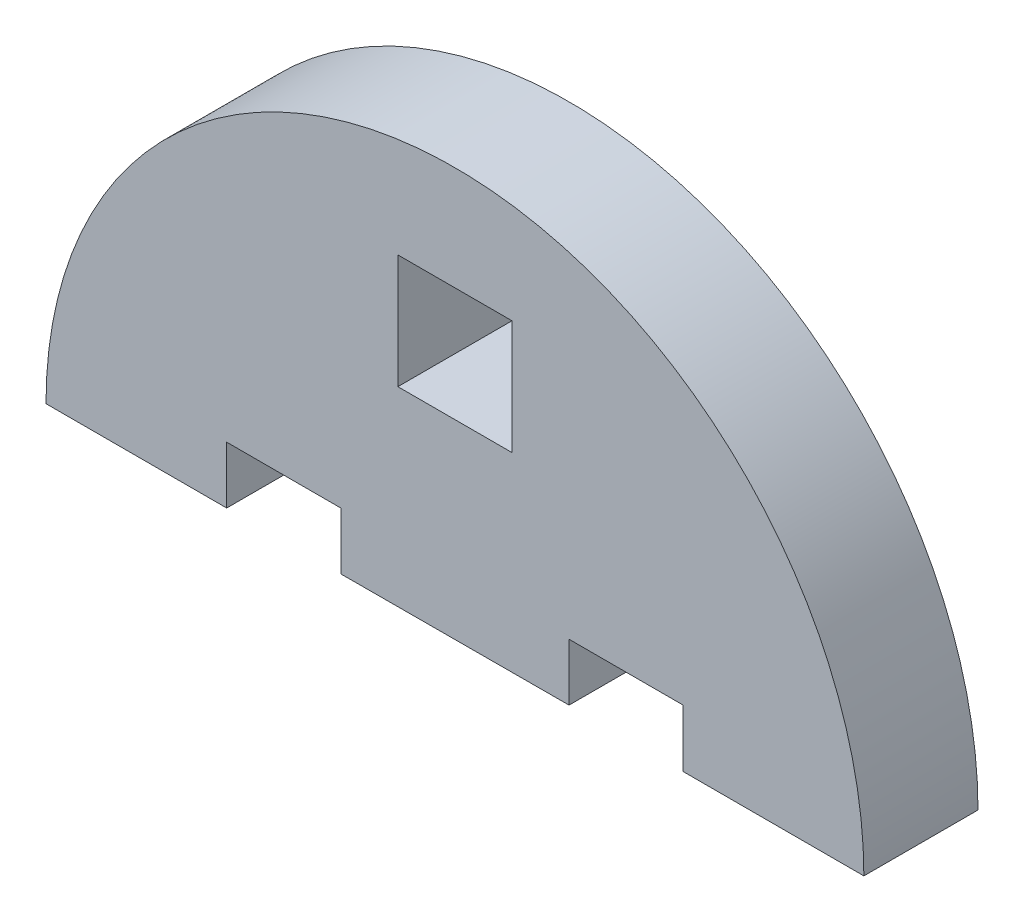
SolidWorks part; units mm, degrees
ref_plane "Front Plane" through (0, 0, 0) normal (0, 0, 1) x (1, 0, 0)
ref_plane "Top Plane" through (0, 0, 0) normal (0, 1, 0) x (1, 0, 0)
ref_plane "Right Plane" through (0, 0, 0) normal (1, 0, 0) x (0, 0, -1)
sketch "Model" plane through (0, 0, 0) normal (0, 0, 1) x (1, 0, 0)
  line L0 (3925.5317, 1073.4879) -> (3916.0317, 1073.4879)
  line L1 (3892.0317, 1073.4879) -> (3882.5317, 1073.4879)
  line L2 (3892.0317, 1073.4879) -> (3892.0317, 1076.4879)
  line L3 (3892.0317, 1076.4879) -> (3898.0317, 1076.4879)
  line L4 (3898.0317, 1076.4879) -> (3898.0317, 1073.4879)
  line L5 (3910.0316, 1073.5139) -> (3910.0316, 1076.5139)
  line L6 (3910.0316, 1076.5139) -> (3916.0316, 1076.5139)
  line L7 (3916.0316, 1076.5139) -> (3916.0317, 1073.4879)
  line L8 (3907.0316, 1089.5139) -> (3901.0316, 1089.5139)
  line L9 (3901.0316, 1089.5139) -> (3901.0316, 1083.5139)
  line L10 (3901.0316, 1083.5139) -> (3907.0316, 1083.5139)
  line L11 (3907.0316, 1083.5139) -> (3907.0316, 1089.5139)
  line L12 (3898.0317, 1073.4879) -> (3910.0316, 1073.5139)
  arc A0 (3925.5317, 1073.4879) -> (3882.5317, 1073.4879) centre (3904.0317, 1073.4879) ccw
extrude "Boss-Extrude1" add sketch "Model" along normal blind 6 contours L10 L11 L8 L9 | A0 L1 L2 L3 L4 L12 L5 L6 L7 L0
